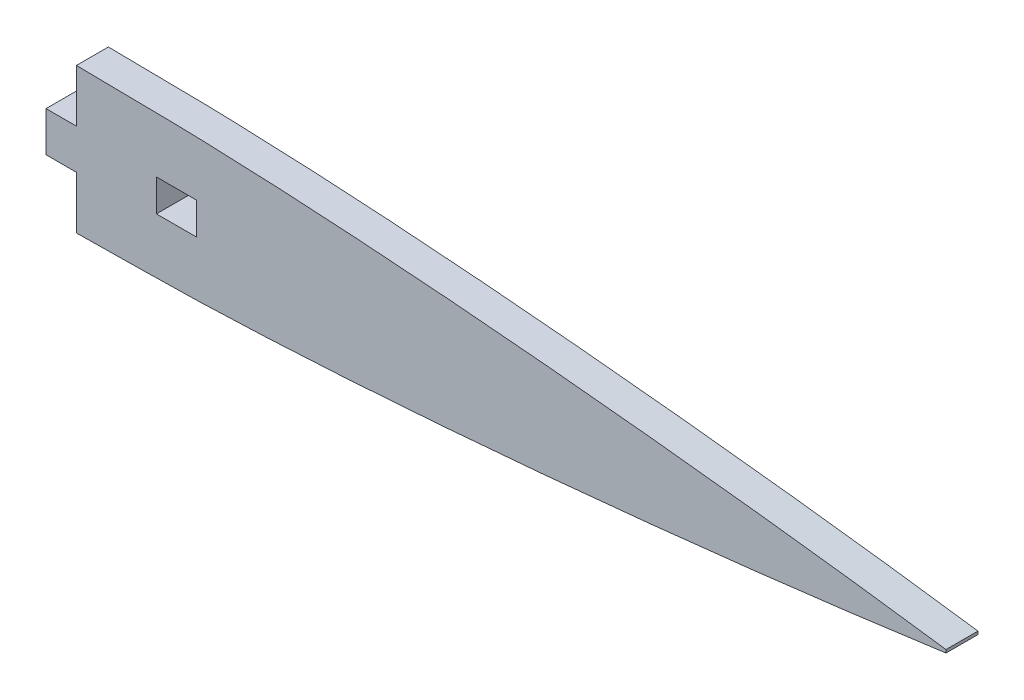
SolidWorks part; units mm, degrees
ref_plane "Front Plane" through (0, 0, 0) normal (0, 0, 1) x (1, 0, 0)
ref_plane "Top Plane" through (0, 0, 0) normal (0, 1, 0) x (1, 0, 0)
ref_plane "Right Plane" through (0, 0, 0) normal (1, 0, 0) x (0, 0, -1)
curve "Curve1"
  spline degree 3 poles (25.4, 0.032, 0) (24.9768, 0.0904, 0) (24.1307, 0.2071, 0) (22.8605, 0.3691, 0) (21.5905, 0.5229, 0) (20.3205, 0.6676, 0) (19.0504, 0.804, 0) (17.7804, 0.9321, 0) (16.5104, 1.0514, 0) (15.2404, 1.1606, 0) (13.9704, 1.2598, 0) (12.692, 1.3473, 0) (11.4135, 1.4221, 0) (10.1349, 1.4776, 0) (8.8649, 1.5185, 0) (7.8146, 1.5178, 0) (6.9766, 1.5373, 0) (6.35, 1.546, 0) (5.715, 1.5506, 0) (5.0799, 1.5478, 0) (4.4448, 1.5346, 0) (3.8095, 1.5078, 0) (3.1738, 1.462, 0) (2.5803, 1.3959, 0) (2.0289, 1.3055, 0) (1.6052, 1.2091, 0) (1.2675, 1.107, 0) (1.012, 1.0136, 0) (0.7549, 0.8965, 0) (0.4933, 0.743, 0) (0.2762, 0.5635, 0) (0.0851, 0.3233, 0) (-0.0556, 0, 0) (0.0851, -0.3233, 0) (0.2762, -0.5635, 0) (0.4933, -0.743, 0) (0.7549, -0.8965, 0) (1.012, -1.0136, 0) (1.2675, -1.107, 0) (1.6052, -1.2091, 0) (2.0289, -1.3055, 0) (2.5803, -1.3959, 0) (3.1738, -1.462, 0) (3.8095, -1.5078, 0) (4.4448, -1.5346, 0) (5.0799, -1.5478, 0) (5.715, -1.5506, 0) (6.35, -1.546, 0) (6.9766, -1.5373, 0) (7.8146, -1.5178, 0) (8.8649, -1.5185, 0) (10.1349, -1.4776, 0) (11.4135, -1.4221, 0) (12.692, -1.3473, 0) (13.9704, -1.2598, 0) (15.2404, -1.1606, 0) (16.5104, -1.0514, 0) (17.7804, -0.9321, 0) (19.0504, -0.804, 0) (20.3205, -0.6676, 0) (21.5905, -0.5229, 0) (22.8605, -0.3691, 0) (24.1307, -0.2071, 0) (24.9768, -0.0904, 0) (25.4, -0.032, 0) knots 0 0 0 0 0.024634 0.049243 0.07383 0.098397 0.122946 0.147479 0.171995 0.196494 0.220976 0.245442 0.27038 0.294813 0.319232 0.343642 0.35536 0.367566 0.379771 0.391975 0.404183 0.416399 0.428636 0.44092 0.450818 0.460843 0.465946 0.471149 0.476523 0.482208 0.488618 0.492568 0.5 0.507432 0.511382 0.517792 0.523477 0.528851 0.534054 0.539157 0.549182 0.55908 0.571364 0.583601 0.595817 0.608025 0.620229 0.632434 0.64464 0.656358 0.680768 0.705187 0.72962 0.754558 0.779024 0.803506 0.828005 0.852521 0.877054 0.901603 0.92617 0.950757 0.975366 1 1 1 1
sketch "Sketch2" plane through (0, 0, 0) normal (0, 0, 1) x (1, 0, 0)
  line L3 (190.5, 0.24) -> (190.5, -0.24)
  line L4 (47.625, -11.59) -> (47.625, 11.59)
  spline S1 degree 3 poles (190.5, 0.24) (187.3257, 0.6779) (180.9805, 1.5531) (171.454, 2.7681) (161.9289, 3.9221) (152.4034, 5.0066) (142.8782, 6.0299) (133.3532, 6.9905) (123.8283, 7.8858) (114.3031, 8.7048) (104.7783, 9.4487) (95.1897, 10.1047) (85.6014, 10.6661) (76.0121, 11.0818) (66.4865, 11.3889) (58.6098, 11.3835) (52.3243, 11.5299) (49.2126, 11.5732) (47.625, 11.59) knots 0 0 0 0 0.024634 0.049243 0.07383 0.098397 0.122946 0.147479 0.171995 0.196494 0.220976 0.245442 0.27038 0.294813 0.319232 0.343642 0.35536 0.367566 0.367566 0.367566 0.367566
  spline S2 degree 3 poles (47.625, -11.59) (49.2126, -11.5732) (52.3243, -11.5299) (58.6098, -11.3835) (66.4865, -11.3889) (76.0121, -11.0818) (85.6014, -10.6661) (95.1897, -10.1047) (104.7783, -9.4487) (114.3031, -8.7048) (123.8283, -7.8858) (133.3532, -6.9905) (142.8782, -6.0299) (152.4034, -5.0066) (161.9289, -3.9221) (171.454, -2.7681) (180.9805, -1.5531) (187.3257, -0.6779) (190.5, -0.24) knots 0.632434 0.632434 0.632434 0.632434 0.64464 0.656358 0.680768 0.705187 0.72962 0.754558 0.779024 0.803506 0.828005 0.852521 0.877054 0.901603 0.92617 0.950757 0.975366 1 1 1 1
  dimension "D1" = 47.625
extrude "Boss-Extrude1" add sketch "Sketch2" along normal blind 5.08
sketch "Sketch3" plane through (0, 0, 0) normal (0, 0, -1) x (-1, 0, 0)
  line L0 (-47.625, 11.59) -> (-47.625, -11.59) construction
  line L1 (-47.625, -11.59) -> (-52.451, -11.59)
  line L2 (-47.625, -11.59) -> (-47.625, -3.175)
  line L3 (-47.625, -3.175) -> (-52.451, -3.175)
  line L4 (-52.451, -11.59) -> (-52.451, -3.175)
  line L5 (-47.625, 3.175) -> (-52.451, 3.175)
  line L6 (-47.625, 3.175) -> (-47.625, 11.59)
  line L7 (-47.625, 11.59) -> (-52.451, 11.59)
  line L8 (-52.451, 3.175) -> (-52.451, 11.59)
  line L9 (-52.451, -3.175) -> (-52.451, 3.175) construction
  line L11 (-65.151, -2.54) -> (-71.501, -2.54)
  line L12 (-65.151, -2.54) -> (-65.151, 2.54)
  line L13 (-65.151, 2.54) -> (-71.501, 2.54)
  line L14 (-71.501, -2.54) -> (-71.501, 2.54)
  point P10 (-47.625, 0)
  point P11 (-65.151, 0)
  point P13 (-52.451, 0)
  point P19 (-47.625, 11.59)
  point P21 (-47.625, -11.59)
  dimension "D1" = 6.35
  dimension "D2" = 4.826
  dimension "D3" = 5.08
  dimension "D4" = 6.35
  dimension "D5" = 12.7
extrude "Cut-Extrude1" cut sketch "Sketch3" against normal through all
